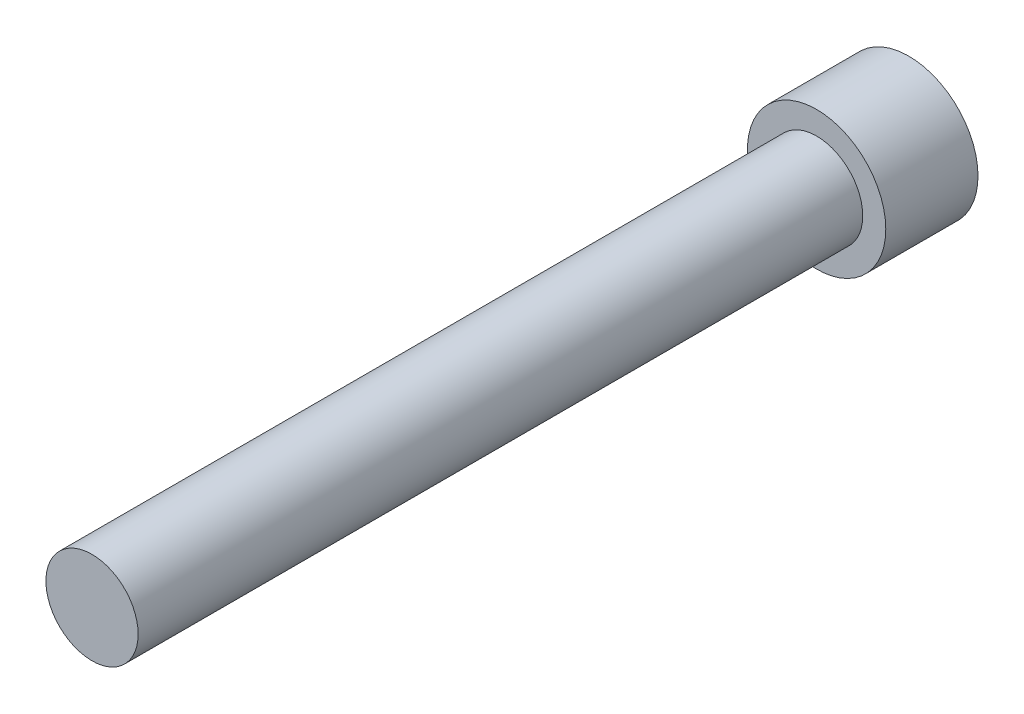
SolidWorks part; units mm, degrees
ref_plane "前视基准面" through (0, 0, 0) normal (0, 0, 1) x (1, 0, 0)
ref_plane "上视基准面" through (0, 0, 0) normal (0, 1, 0) x (1, 0, 0)
ref_plane "右视基准面" through (0, 0, 0) normal (1, 0, 0) x (0, 0, -1)
sketch "草图1" plane through (0, 0, 0) normal (0, 0, 1) x (1, 0, 0)
  circle A0 centre (-16.4105, 16.545) radius 10.5
extrude "凸台-拉伸1" add sketch "草图1" along normal blind 14
ref_point "点1"
sketch "草图2" plane through (0, 0, 14) normal (0, 0, 1) x (1, 0, 0)
  circle A0 centre (-16.4105, 16.545) radius 7
extrude "凸台-拉伸2" add sketch "草图2" along normal blind 110
